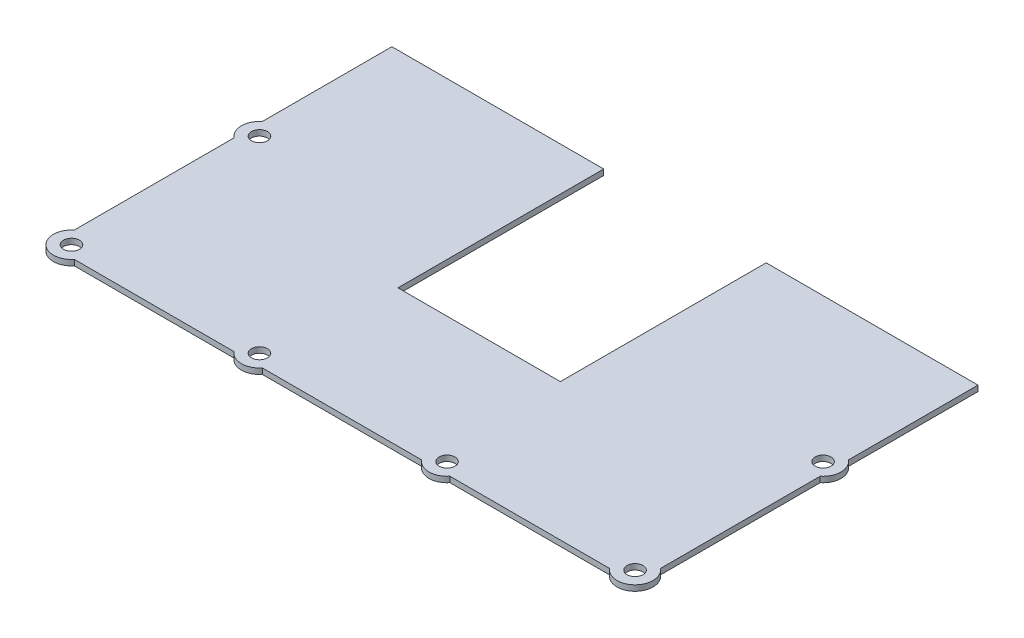
SolidWorks part; units mm, degrees
material "UHMW"
ref_plane "Front Plane" through (0, 0, 0) normal (0, 0, 1) x (1, 0, 0)
ref_plane "Top Plane" through (0, 0, 0) normal (0, 1, 0) x (1, 0, 0)
ref_plane "Right Plane" through (0, 0, 0) normal (1, 0, 0) x (0, 0, -1)
sketch "Sketch1" plane through (0, 0, 0) normal (0, 1, 0) x (1, 0, 0)
  circle A0 centre (3.175, -40.4401) radius 2.2479
  circle A1 centre (3.175, -93.3568) radius 2.2479
  circle A2 centre (56.0917, -93.3568) radius 2.2479
  circle A3 centre (108.8828, -93.3568) radius 2.2479
  circle A4 centre (161.7995, -93.3568) radius 2.2479
  circle A5 centre (161.7995, -40.4401) radius 2.2479
  line B0 (59.6265, 0) -> (0, 0)
  line B1 (59.6265, 0) -> (59.6265, -57.9238)
  line B2 (164.9745, -36.4745) -> (164.9745, 0)
  line B3 (164.9745, -89.3912) -> (164.9745, -44.4057)
  line B4 (112.8484, -96.5318) -> (157.8339, -96.5318)
  line B5 (101.6, -96.5318) -> (104.9173, -96.5318)
  line B6 (101.6, -96.5318) -> (95.25, -96.5318)
  line B7 (69.85, -96.5318) -> (95.25, -96.5318)
  line B8 (69.85, -96.5318) -> (63.5, -96.5318)
  line B9 (60.0572, -96.5318) -> (63.5, -96.5318)
  line B10 (7.1406, -96.5318) -> (52.1261, -96.5318)
  line B11 (0, -44.4057) -> (0, -89.3912)
  line B12 (0, 0) -> (0, -36.4745)
  line B13 (164.9745, 0) -> (105.348, 0)
  line B14 (105.348, 0) -> (105.348, -57.9238)
  line B15 (59.6265, -57.9238) -> (105.348, -57.9238)
  arc B16 (164.9745, -44.4057) -> (164.9745, -36.4745) centre (161.7995, -40.4401) ccw
  arc B17 (157.8339, -96.5318) -> (164.9745, -89.3912) centre (161.7995, -93.3568) ccw
  arc B18 (104.9173, -96.5318) -> (112.8484, -96.5318) centre (108.8828, -93.3568) ccw
  arc B19 (52.1261, -96.5318) -> (60.0572, -96.5318) centre (56.0917, -93.3568) ccw
  arc B20 (0, -89.3912) -> (7.1406, -96.5318) centre (3.175, -93.3568) ccw
  arc B21 (0, -36.4745) -> (0, -44.4057) centre (3.175, -40.4401) ccw
  dimension "D1" = 4.4958
sketch_block_instance "Block-topplate-1"
sketch_block "Block-topplate" parameters "D1"=72.8218, "D2"=72.8218, "D3"=25.4
extrude "Boss-Extrude1" add sketch "Sketch1" along normal blind 1.5875
equation "\"Unit Measure\"= \"BoundingVolume\" / \"Thickness\"'in^2"
